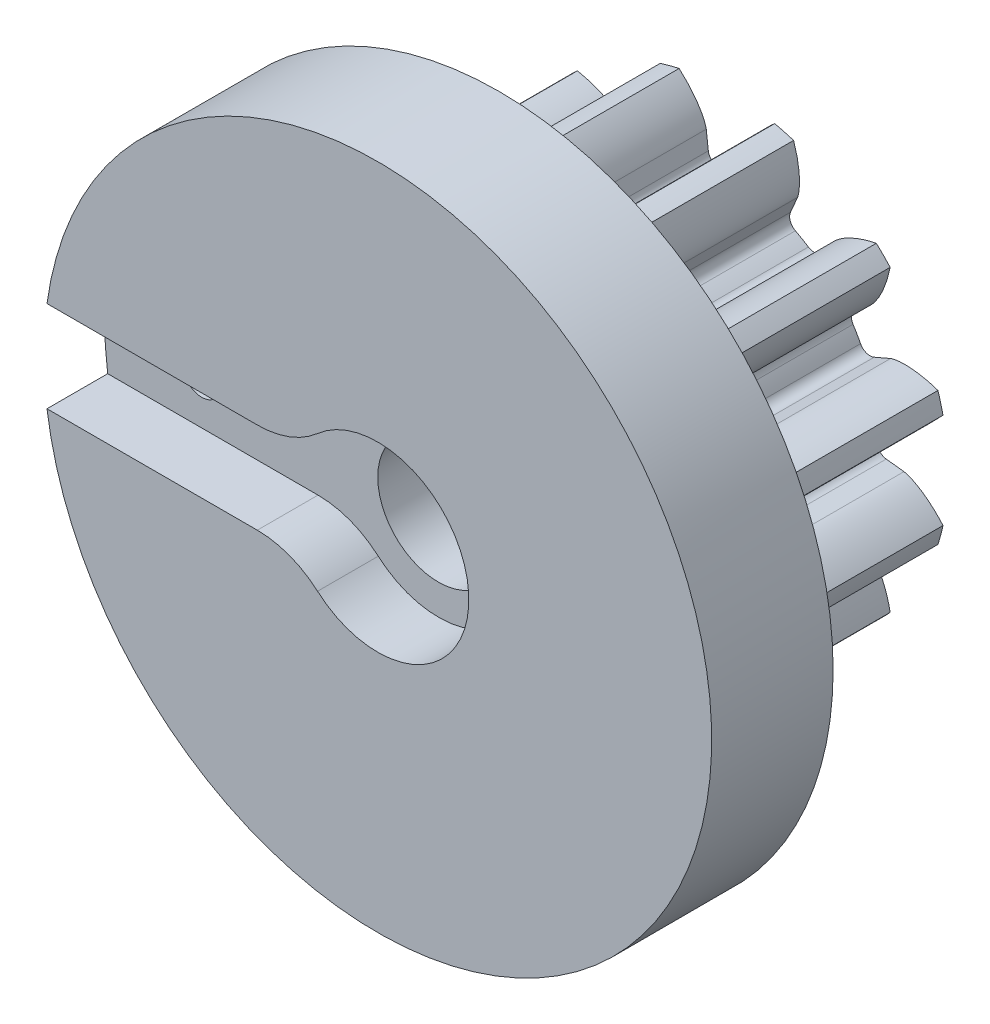
SolidWorks part; units mm, degrees
ref_plane "Front Plane" through (0, 0, 0) normal (0, 0, 1) x (1, 0, 0)
ref_plane "Top Plane" through (0, 0, 0) normal (0, 1, 0) x (1, 0, 0)
ref_plane "Right Plane" through (0, 0, 0) normal (1, 0, 0) x (0, 0, -1)
sketch "Sketch1" plane through (0, 0, 0) normal (0, 0, 1) x (1, 0, 0)
  line L0 (0, 0) -> (0, 6.35) construction
  line L1 (-2.0409, 7.0928) -> (2.0409, 5.6072) construction
  circle A0 centre (0, 0) radius 5.0271 construction
  circle A1 centre (0, 0) radius 7.4083 construction
  circle A2 centre (0, 0) radius 6.35 construction
  circle A3 centre (0, 0) radius 5.967 construction
  circle A4 centre (0, 0) radius 2.3813 construction
  circle A5 centre (0, 0) radius 4.826 construction
  point P8 (304.8, 0)
  point P13 (152.4, 0)
  dimension "OD | Outside Diameter" = 14.8167
  dimension "Root Diameter" = 10.0542
  dimension "Gear Pitch Diameter" = 12.7
  dimension "Base Diameter" = 11.9341
  dimension "For Shaft Diameter" = 4.7625
  dimension "Hub Diameter" = 9.652
  dimension "Pressure Angle" = 20
  dimension "Number of Teeth" = 304.8
  dimension "Gear Pitch | Diametral Pitch" = 609.6
sketch "Sketch2" plane through (0, 0, 0) normal (1, 0, 0) x (0, 0, -1)
  line L0 (-6.35, 0) -> (6.35, 0) construction
  line L1 (-6.35, 7.4083) -> (6.35, 7.4083) construction
  point P2 (0, 7.4083)
  point P4 (0, 0)
  point P6 (0, 7.4083)
  dimension "Overall Width" = 12.7
  dimension "Hub Width" = 6.35
  dimension "Face Width" = 6.35
sketch "Sketch3" plane through (0, 0, 0) normal (0, 0, 1) x (1, 0, 0)
  circle A0 centre (0, 0) radius 7.4083
  circle A1 centre (0, 0) radius 7.4083 construction
extrude "Boss-Extrude1" add sketch "Sketch3" against normal blind 7.62
sketch "Sketch4" plane through (0, 0, 0) normal (0, 0, 1) x (1, 0, 0)
  line L0 (0, 0) -> (4.9933, 0.5818) construction
  line L2 (0, 0) -> (4.9933, -0.5818) construction
  line L4 (4.9933, 0.5818) -> (5.927, 0.6906)
  line L5 (5.927, -0.6906) -> (4.9933, -0.5818)
  arc A0 (4.9933, 0.5818) -> (4.9933, -0.5818) centre (0, 0) cw
  arc A3 (7.2339, 1.5983) -> (7.2339, -1.5983) centre (0, 0) cw
  circle A4 centre (0, 0) radius 7.4083 construction
  spline S0 degree 4 poles (5.927, 0.6906) (5.9293, 0.6909) (5.9359, 0.6919) (5.9484, 0.6942) (5.9686, 0.6987) (5.9942, 0.7052) (6.0271, 0.7148) (6.0655, 0.7275) (6.1073, 0.7428) (6.1523, 0.761) (6.1969, 0.7804) (6.2409, 0.8011) (6.2844, 0.8228) (6.3367, 0.8503) (6.3986, 0.8852) (6.47, 0.9285) (6.5497, 0.9807) (6.6294, 1.0371) (6.7066, 1.0952) (6.7832, 1.1568) (6.8562, 1.2185) (6.9304, 1.2856) (6.9981, 1.3489) (7.0721, 1.4232) (7.1312, 1.484) (7.2071, 1.5675) (7.2513, 1.6179) (7.3023, 1.6779) (7.3245, 1.7051) (7.3382, 1.7219) knots 0 0 0 0 0 0.005377 0.015084 0.028532 0.04661 0.064855 0.092111 0.119476 0.146842 0.174209 0.201575 0.228941 0.256307 0.307035 0.361767 0.4165 0.471232 0.525964 0.580697 0.635429 0.690161 0.744894 0.799626 0.854358 0.909091 0.954545 1 1 1 1 1 construction
  spline S1 degree 4 poles (5.927, 0.6906) (5.9293, 0.6909) (5.9359, 0.6919) (5.9484, 0.6942) (5.9686, 0.6987) (5.9942, 0.7052) (6.0271, 0.7148) (6.0655, 0.7275) (6.1073, 0.7428) (6.1523, 0.761) (6.1969, 0.7804) (6.2409, 0.8011) (6.2844, 0.8228) (6.3367, 0.8503) (6.3986, 0.8852) (6.47, 0.9285) (6.5497, 0.9807) (6.6294, 1.0371) (6.7066, 1.0952) (6.7832, 1.1568) (6.8562, 1.2185) (6.9304, 1.2856) (6.9981, 1.3489) (7.0721, 1.4232) (7.1312, 1.484) (7.1906, 1.5494) (7.2193, 1.5816) (7.2339, 1.5983) knots 0 0 0 0 0 0.005377 0.015084 0.028532 0.04661 0.064855 0.092111 0.119476 0.146842 0.174209 0.201575 0.228941 0.256307 0.307035 0.361767 0.4165 0.471232 0.525964 0.580697 0.635429 0.690161 0.744894 0.799626 0.854358 0.909091 0.909091 0.909091 0.909091 0.909091
  spline S2 degree 4 poles (5.927, -0.6906) (5.9293, -0.6909) (5.9359, -0.6919) (5.9484, -0.6942) (5.9686, -0.6987) (5.9942, -0.7052) (6.0271, -0.7148) (6.0655, -0.7275) (6.1073, -0.7428) (6.1523, -0.761) (6.1969, -0.7804) (6.2409, -0.8011) (6.2844, -0.8228) (6.3367, -0.8503) (6.3986, -0.8852) (6.47, -0.9285) (6.5497, -0.9807) (6.6294, -1.0371) (6.7066, -1.0952) (6.7832, -1.1568) (6.8562, -1.2185) (6.9304, -1.2856) (6.9981, -1.3489) (7.0721, -1.4232) (7.1312, -1.484) (7.2071, -1.5675) (7.2513, -1.6179) (7.3023, -1.6779) (7.3245, -1.7051) (7.3382, -1.7219) knots 0 0 0 0 0 0.005377 0.015084 0.028532 0.04661 0.064855 0.092111 0.119476 0.146842 0.174209 0.201575 0.228941 0.256307 0.307035 0.361767 0.4165 0.471232 0.525964 0.580697 0.635429 0.690161 0.744894 0.799626 0.854358 0.909091 0.954545 1 1 1 1 1 construction
  spline S3 degree 4 poles (5.927, -0.6906) (5.9293, -0.6909) (5.9359, -0.6919) (5.9484, -0.6942) (5.9686, -0.6987) (5.9942, -0.7052) (6.0271, -0.7148) (6.0655, -0.7275) (6.1073, -0.7428) (6.1523, -0.761) (6.1969, -0.7804) (6.2409, -0.8011) (6.2844, -0.8228) (6.3367, -0.8503) (6.3986, -0.8852) (6.47, -0.9285) (6.5497, -0.9807) (6.6294, -1.0371) (6.7066, -1.0952) (6.7832, -1.1568) (6.8562, -1.2185) (6.9304, -1.2856) (6.9981, -1.3489) (7.0721, -1.4232) (7.1312, -1.484) (7.1906, -1.5494) (7.2193, -1.5816) (7.2339, -1.5983) knots 0 0 0 0 0 0.005377 0.015084 0.028532 0.04661 0.064855 0.092111 0.119476 0.146842 0.174209 0.201575 0.228941 0.256307 0.307035 0.361767 0.4165 0.471232 0.525964 0.580697 0.635429 0.690161 0.744894 0.799626 0.854358 0.909091 0.909091 0.909091 0.909091 0.909091
  dimension "D1" = 10.0542
extrude "Cut-Extrude1" cut sketch "Sketch4" against normal through all both and the other way through all
fillet "Fillet1" radius 0.3551 2 edges at (4.9933, -0.5818, -3.81) (4.9933, 0.5818, -3.81)
pattern_circular "CirPattern1" count 12 over 360 about axis through (0, 0, 6.35) along (0, 0, -1) of "Cut-Extrude1", "Fillet1"
scale "Scale1" bodies to scale 106 scale about origin uniform scaling yes scale factor 2.5
sketch "Sketch10" plane through (0, 0, 0) normal (0, 0, 1) x (1, 0, 0)
  circle A0 centre (0, 0) radius 27.94
  dimension "D1" = 55.88
extrude "Boss-Extrude4" add sketch "Sketch10" along normal blind 10.16
sketch "Sketch11" plane through (0, 0, -19.05) normal (0, 0, -1) x (-1, 0, 0)
  circle A0 centre (0, 0) radius 5.08
  dimension "D1" = 10.16
extrude "Cut-Extrude5" cut sketch "Sketch11" against normal through all
sketch "Sketch12" plane through (0, 0, 10.16) normal (0, 0, 1) x (1, 0, 0)
  line L1 (-10.0803, -3.81) -> (-28.4386, -3.81)
  line L3 (-10.0803, 3.81) -> (-28.4386, 3.81)
  line L4 (-28.4386, -3.81) -> (-28.4386, 3.81)
  arc A0 (-5.0402, -5.715) -> (-5.0402, 5.715) centre (0, 0) ccw
  arc A1 (-10.0803, -3.81) -> (-5.0402, -5.715) centre (-10.0803, -11.43) cw
  arc A2 (-10.0803, 3.81) -> (-5.0402, 5.715) centre (-10.0803, 11.43) ccw
  point P10 (-28.4386, 0)
  dimension "D1" = 7.62
  dimension "D2" = 7.62
  dimension "D3" = 7.62
extrude "Cut-Extrude6" cut sketch "Sketch12" against normal blind 5.08
sketch "Sketch13" plane through (0, 0, 5.08) normal (0, 0, 1) x (1, 0, 0)
  line L0 (0, 0) -> (0, 18.2969) construction
  circle A0 centre (-19.812, 0) radius 1.5875
  dimension "D1" = 3.175
  dimension "D2" = 19.812
extrude "Cut-Extrude12" cut sketch "Sketch13" against normal through all
sketch "Sketch16" plane through (0, 0, 0) normal (0, 0, -1) x (-1, 0, 0)
  circle A0 centre (19.812, 0) radius 2.7496
  dimension "D1" = 5.4991
extrude "Cut-Extrude13" cut sketch "Sketch16" against normal blind 3.81
sketch "Sketch17" plane through (0, 0, -19.05) normal (0, 0, -1) x (-1, 0, 0)
  circle A0 centre (0, 0) radius 12.7
  dimension "D1" = 25.4
equation "\"Root Diameter@Sketch1\"=\"Root Diameter\""
equation "\"OD | Outside Diameter@Sketch1\"=\"Outside Diameter\""
equation "\"D1@CirPattern1\"=\"Number of Teeth\""
equation "\"Diametral Pitch\"= 24"
equation "\"Number of Teeth\"= 12"
equation "\"Pressure Angle\"=20"
equation "\"Pitch Diameter\"= \"Number of Teeth\" / \"Diametral Pitch\""
equation "\"Base Diameter\"= \"Pitch Diameter\" * cos ( \"Pressure Angle\" )"
equation "\"Outside Diameter\"= ( \"Number of Teeth\" + 2 ) / \"Diametral Pitch\""
equation "\"Dedendum\"= 1.25 / \"Diametral Pitch\""
equation "\"Root Diameter\"= \"Pitch Diameter\" - ( 2 * \"Dedendum\" )"
equation "\"Pitch Angle\"= 360deg / \"Number of Teeth\""
equation "\"Alpha\"= sqr ( \"Pitch Diameter\" ^ 2 - \"Base Diameter\" ^ 2 ) / \"Base Diameter\" * 180 / PI - \"Pressure Angle\""
equation "\"Beta\"= ( \"Pitch Angle\" / 4 - \"Alpha\" )"
equation "\"Phi\"= sqr ( ( \"Outside Diameter\" / 2 ) ^ 2 - ( \"Base Diameter\" / 2 ) ^ 2 ) / ( \"Base Diameter\" / 2 )"
equation "\"Addendum\"= 1 / \"Diametral Pitch\""
equation "\"WorkingDepth\"= 2 / \"Diametral Pitch\""
equation "\"WholeDepth\"= 2.25 / \"Diametral Pitch\""
equation "\"Clearance\"= 0.25 / \"Diametral Pitch\""
equation "\"ToothThickness\"= ( pi * 2 ) / \"Diametral Pitch\""
equation "\"CircularPitch\"= pi / \"Diametral Pitch\""
equation "\"Number of Teeth@Sketch1\"=\"Number of Teeth\""
equation "\"Gear Pitch | Diametral Pitch@Sketch1\"=\"Diametral Pitch\""
equation "\"Pressure Angle@Sketch1\"=\"Pressure Angle\""
equation "\"Gear Pitch Diameter@Sketch1\"=\"Pitch Diameter\""
equation "\"Base Diameter@Sketch1\"=\"Base Diameter\""
equation "\"Fillet\"= \"Clearance\" * cos ( \"Pressure Angle\" ) * tan ( ( 90 + \"Pressure Angle\" ) / 2 )"
equation "\"D1@Fillet1\"=\"Fillet\""
equation "\"D1@Sketch4\"=if( \"Base Diameter\">\"Root Diameter\",\"Root Diameter\",\"Base Diameter\"-.00001)"
equation "\"D1@Fillet2\"=\"Fillet\""
